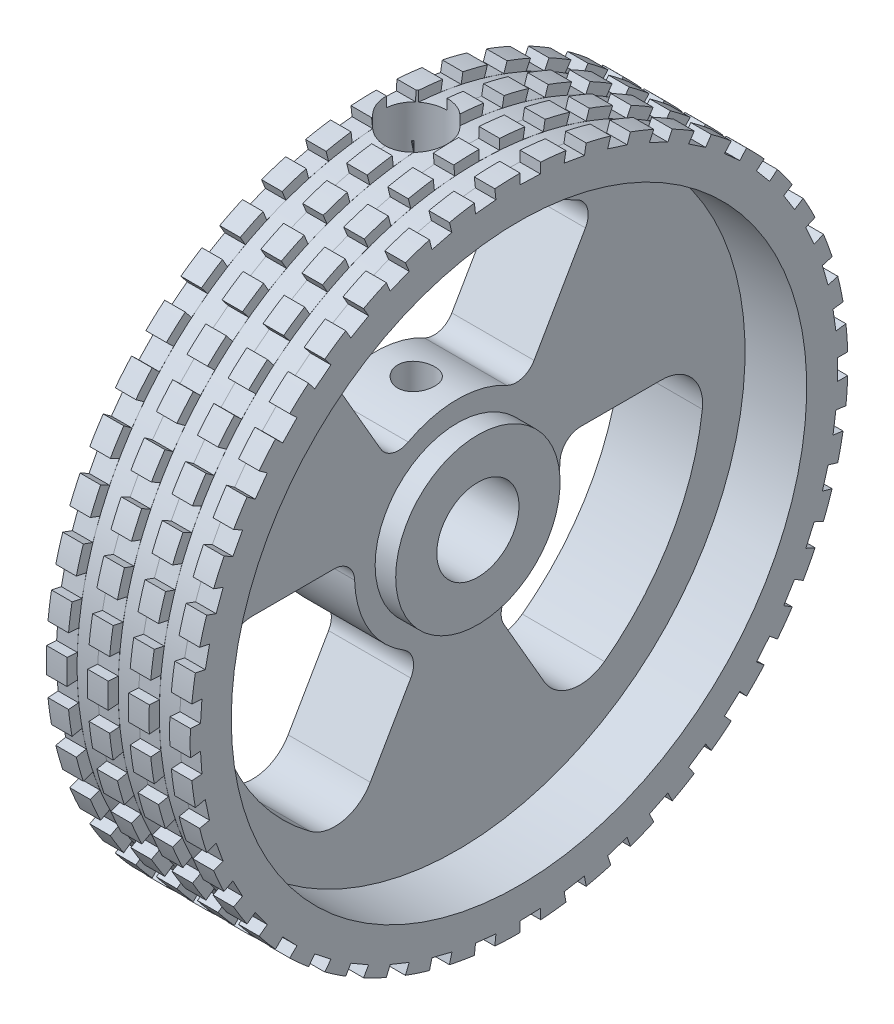
SolidWorks part; units mm, degrees
ref_plane "Front Plane" through (0, 0, 0) normal (0, 0, 1) x (1, 0, 0)
ref_plane "Top Plane" through (0, 0, 0) normal (0, 1, 0) x (1, 0, 0)
ref_plane "Right Plane" through (0, 0, 0) normal (1, 0, 0) x (0, 0, -1)
sketch "Sketch1" plane through (0, 0, 0) normal (0, 0, 1) x (1, 0, 0)
  line L0 (0, 0) -> (6.5, 0) construction
  line L1 (0, 0) -> (0, 2) construction
  line L2 (0, 2) -> (0, 16)
  line L3 (0, 16) -> (7, 16)
  line L4 (7, 16) -> (7, 14)
  line L5 (7, 14) -> (4, 14)
  line L6 (4, 14) -> (4, 4)
  line L7 (4, 4) -> (5, 4)
  line L8 (5, 4) -> (5, 2)
  line L9 (5, 2) -> (0, 2)
  dimension "D1" = 4
  dimension "D2" = 7
  dimension "D3" = 5
  dimension "D4" = 32
  dimension "D5" = 28
  dimension "D6" = 8
  dimension "D7" = 4
revolve "Revolve1" add sketch "Sketch1" angle 360 about L0
sketch "Sketch2" plane through (0, 0, 0) normal (0, 0, 1) x (1, 0, 0)
  line L0 (2, 0) -> (2, 21.3185) construction
  line L1 (0, 16) -> (0, -16) construction
  line L2 (3.5, 16) -> (3.5, 11.3535)
  line L3 (2, 0) -> (2, 16)
  line L4 (3.5, 11.3535) -> (2.9, 11.3535)
  line L5 (2.9, 11.3535) -> (2.9, 0)
  line L6 (2.9, 0) -> (2, 0)
  line L7 (7, 16) -> (0, 16) construction
  line L8 (2, 16) -> (3.5, 16)
  line L9 (0, 0) -> (2, 0) construction
  dimension "D1" = 2
  dimension "D2" = 3
  dimension "D3" = 1.8
  dimension "D4" = 4.6465
revolve "Cut-Revolve1" cut sketch "Sketch2" angle 360 about L3
sketch "Sketch3" plane through (0, 0, 0) normal (0, 0, 1) x (1, 0, 0)
  line L5 (7, 16) -> (3.5, 16) construction
  line L6 (5, 16) -> (6, 16)
  line L7 (5, 16) -> (5, 15.5)
  line L8 (5, 15.5) -> (6, 15.5)
  line L9 (6, 16) -> (6, 15.5)
  line L10 (7, -16) -> (7, 16) construction
  line L11 (0, 0) -> (11.7344, 0) construction
  dimension "D1" = 0.5
  dimension "D2" = 1
  dimension "D3" = 1
revolve "Cut-Revolve2" cut sketch "Sketch3" angle 360 about L11
sketch "Sketch9" plane through (4, 0, 0) normal (1, 0, 0) x (0, 0, -1)
  line L0 (0, 0) -> (18.9933, 0) construction
  line L2 (16.5, 0.5) -> (15.5, 0.5)
  line L3 (16.5, 0.5) -> (16.5, -0.5)
  line L4 (16.5, -0.5) -> (15.5, -0.5)
  line L5 (15.5, 0.5) -> (15.5, -0.5)
  line L6 (16.5, 0.5) -> (15.5, -0.5) construction
  line L7 (16.5, -0.5) -> (15.5, 0.5) construction
  circle A0 centre (0, 0) radius 16 construction
  point P3 (16, 0)
  dimension "D1" = 1
  dimension "D2" = 1
  dimension "D3" = 16
extrude "Cut-Extrude5" cut sketch "Sketch9" against normal blind 10 and the other way blind 10
pattern_circular "CirPattern1" count 45 over 360 about axis through (0, 0, 0) along (1, 0, 0) of "Cut-Extrude5"
pattern_linear "LPattern1" count 3 spacing 2 along (-1, 0, 0) of "Cut-Revolve2"
sketch "Sketch12" plane through (4, 0, 0) normal (1, 0, 0) x (0, 0, -1)
  line L0 (5.2509, -10.7902) -> (1.7297, -4.6913)
  line L1 (4.9276, 0.8477) -> (11.97, 0.8477)
  arc A0 (5.2509, -10.7902) -> (11.97, 0.8477) centre (0, 0) ccw
  arc A1 (4.9276, 0.8477) -> (1.7297, -4.6913) centre (0, 0) cw
  dimension "D1" = 12
  dimension "D2" = 5
  dimension "D3" = 60
extrude "Cut-Extrude6" cut sketch "Sketch12" against normal blind 10
fillet "Fillet3" radius 1 2 edges at (2, -4.6913, -1.7297) (2, 0.8477, -4.9276)
fillet "Fillet4" radius 2 2 edges at (2, -10.7902, -5.2509) (2, 0.8477, -11.97)
pattern_circular "CirPattern2" count 3 over 360 about axis through (0, 0, 0) along (1, 0, 0) of "Cut-Extrude6"
fillet "Fillet5" radius 1 4 edges at (2, 3.8436, 3.1979) (2, 0.8477, 4.9276) (2, -4.6913, 1.7297) (2, 9.9425, -6.7191)
fillet "Fillet6" radius 1 1 edges at (2, 3.8436, -3.1979)
fillet "Fillet7" radius 2 3 edges at (2, 9.9425, 6.7191) (2, 0.8477, 11.97) (2, -10.7902, 5.2509)
